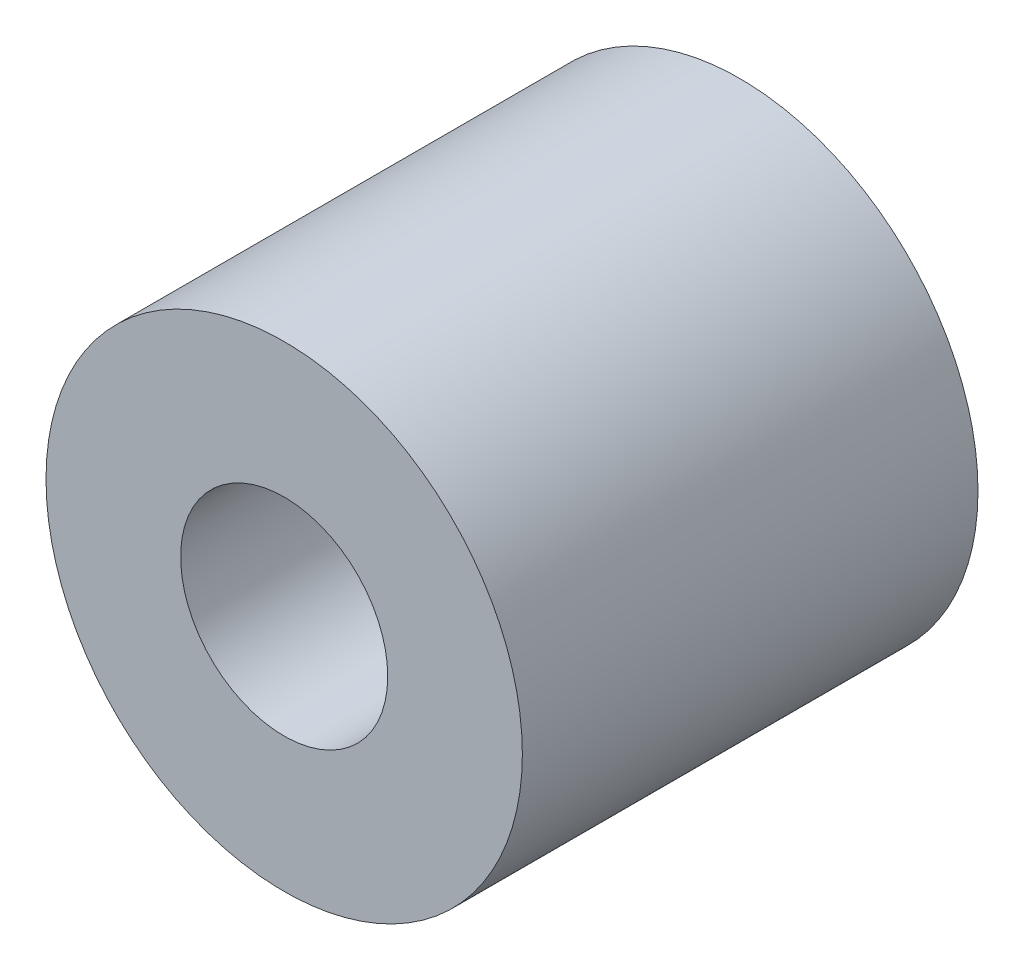
SolidWorks part; units mm, degrees
material "Alumine"
ref_plane "Plan de face" through (0, 0, 0) normal (0, 0, 1) x (1, 0, 0)
ref_plane "Plan de dessus" through (0, 0, 0) normal (0, 1, 0) x (1, 0, 0)
ref_plane "Plan de droite" through (0, 0, 0) normal (1, 0, 0) x (0, 0, -1)
sketch "Esquisse1" plane through (0, 0, 0) normal (0, 0, 1) x (1, 0, 0)
  circle A0 centre (0, 0) radius 5
  circle A1 centre (0, 0) radius 11.5
  dimension "D1" = 10
  dimension "D2" = 23
extrude "Boss.-Extru.1" add sketch "Esquisse1" along normal blind 22
